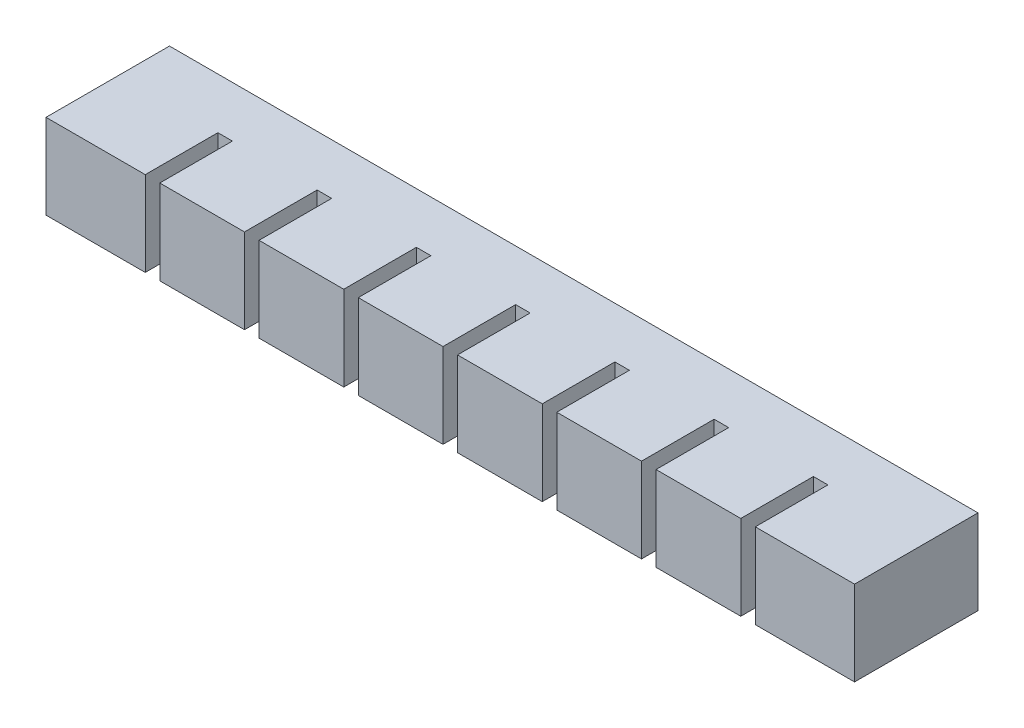
SolidWorks part; units mm, degrees
ref_plane "Front Plane" through (0, 0, 0) normal (0, 0, 1) x (1, 0, 0)
ref_plane "Top Plane" through (0, 0, 0) normal (0, 1, 0) x (1, 0, 0)
ref_plane "Right Plane" through (0, 0, 0) normal (1, 0, 0) x (0, 0, -1)
sketch "Sketch3" plane through (0, 0, 0) normal (0, 0, 1) x (1, 0, 0)
  line L1 (0, 0) -> (17.5, 0)
  line L2 (0, 0) -> (0, 17.5)
  line L3 (0, 17.5) -> (17.5, 17.5)
  line L4 (17.5, 0) -> (17.5, 17.5)
  dimension "D1" = 17.5
  dimension "D2" = 17.5
extrude "Boss-Extrude2" add sketch "Sketch3" along normal blind 20
sketch "Sketch4" plane through (0, 0, 0) normal (0, 0, -1) x (-1, 0, 0)
  line L0 (0, 17.5) -> (0, 0) construction
  line L1 (-13.5, 13.5) -> (-4, 13.5)
  line L2 (-13.5, 13.5) -> (-13.5, 4)
  line L3 (-13.5, 4) -> (-4, 4)
  line L4 (-4, 13.5) -> (-4, 4)
  line L5 (-17.5, 17.5) -> (0, 17.5) construction
  line L6 (0, 0) -> (-17.5, 0) construction
  line L7 (-17.5, 0) -> (-17.5, 17.5) construction
  dimension "D1" = 4
  dimension "D2" = 4
  dimension "D3" = 4
  dimension "D4" = 4
extrude "Cut-Extrude1" cut sketch "Sketch4" against normal blind 16
sketch "Sketch5" plane through (0, 0, 0) normal (-1, 0, 0) x (0, 0, 1)
  line L0 (20, 0) -> (0, 0) construction
  line L1 (0, 17.5) -> (5, 17.5)
  line L2 (0, 17.5) -> (0, 0)
  line L3 (0, 0) -> (5, 0)
  line L4 (5, 17.5) -> (5, 0)
  dimension "D1" = 5
extrude "Boss-Extrude3" add sketch "Sketch5" along normal blind 3
pattern_linear "LPattern1" count 8 spacing 20.5 along (-1, 0, 0) of bodies 104
combine bodies "Combine1" operation type add bodies to combine 105 106 107 104 108 109 110 111
sketch "Sketch6" plane through (-143.5, 0, 0) normal (-1, 0, 0) x (0, 0, 1)
  line L1 (5, 17.5) -> (20, 17.5)
  line L2 (5, 17.5) -> (5, 0)
  line L3 (5, 0) -> (20, 0)
  line L4 (20, 17.5) -> (20, 0)
extrude "Boss-Extrude4" add sketch "Sketch6" along normal up to surface (3 mm away) up to face at (-146.5, 8.75, 2.5)
sketch "Sketch7" plane through (17.5, 0, 0) normal (1, 0, 0) x (0, 0, -1)
  line L1 (0, 17.5) -> (-20, 17.5)
  line L2 (0, 17.5) -> (0, 0)
  line L3 (0, 0) -> (-20, 0)
  line L4 (-20, 17.5) -> (-20, 0)
extrude "Boss-Extrude5" add sketch "Sketch7" along normal blind 3
ref_point "Point1"
sketch "Sketch8" plane through (0, 0, 0) normal (0, 0, -1) x (-1, 0, 0)
  line L0 (130, 13.5) -> (130, 4) construction
  line L1 (-4, 7.75) -> (130, 7.75)
  line L2 (-4, 7.75) -> (-4, 9.75)
  line L3 (-4, 9.75) -> (130, 9.75)
  line L4 (130, 7.75) -> (130, 9.75)
  line L5 (-4, 7.75) -> (130, 9.75) construction
  line L6 (-4, 9.75) -> (130, 7.75) construction
  point P0 (63, 8.75)
  dimension "D1" = 2
extrude "Cut-Extrude2" cut sketch "Sketch8" against normal blind 2
sketch "Sketch9" plane through (0, 0, 0) normal (0, 0, -1) x (-1, 0, 0)
  line L1 (-20.5, 17.5) -> (146.5, 17.5)
  line L2 (-20.5, 17.5) -> (-20.5, 0)
  line L3 (-20.5, 0) -> (146.5, 0)
  line L4 (146.5, 17.5) -> (146.5, 0)
extrude "Boss-Extrude6" add sketch "Sketch9" along normal blind 5.5
